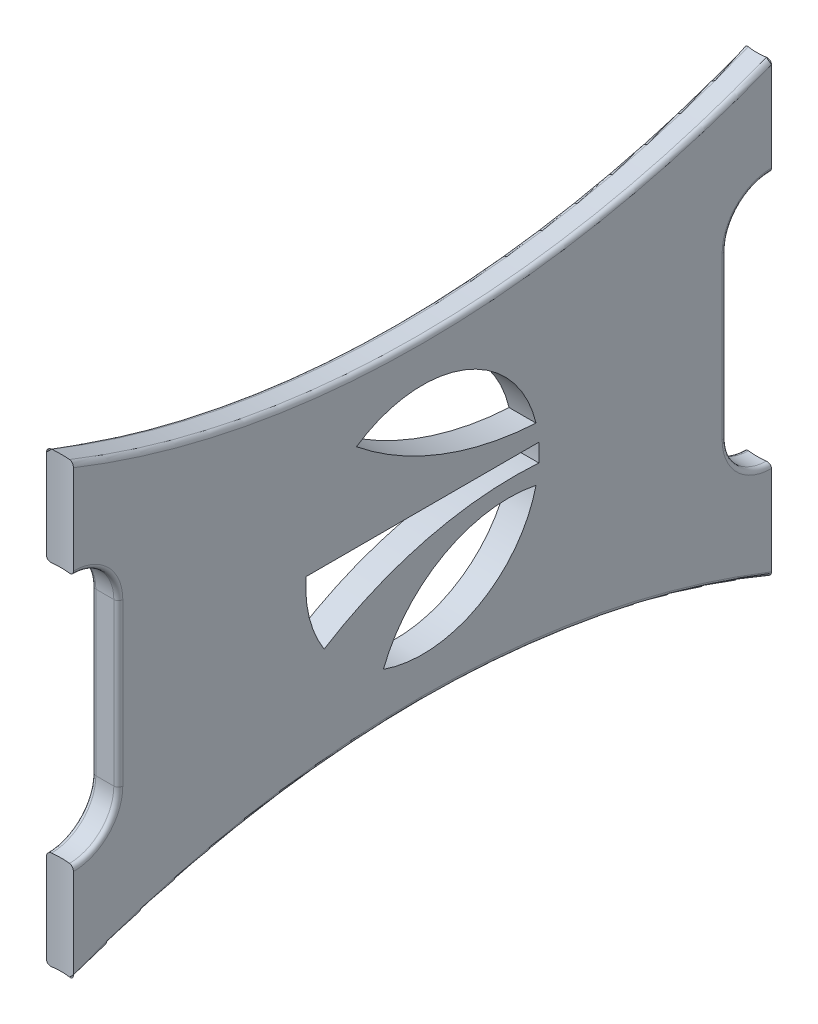
SolidWorks part; units mm, degrees
ref_plane "Plan de face" through (0, 0, 0) normal (0, 0, 1) x (1, 0, 0)
ref_plane "Plan de dessus" through (0, 0, 0) normal (0, 1, 0) x (1, 0, 0)
ref_plane "Plan de droite" through (0, 0, 0) normal (1, 0, 0) x (0, 0, -1)
sketch "Esquisse1" plane through (0, 0, 0) normal (0, 1, 0) x (1, 0, 0)
  line L0 (0, 0) -> (7.2264, 0) construction
  line L1 (0, 0) -> (0, 41.9928) construction
  line L4 (-1.5, 38.8834) -> (-1.5, -38.8834)
  line L6 (1.5, 38.8834) -> (1.5, -38.8834)
  arc A0 (-1.5, 38.8834) -> (1.5, 38.8834) centre (0, 47.25) ccw
  arc A1 (-1.5, -38.8834) -> (1.5, -38.8834) centre (0, -47.25) cw
  dimension "D2" = 8.5
  dimension "D3" = 94.5
  dimension "D1" = 3
extrude "Extrusion1" add sketch "Esquisse1" along normal mid plane 50
sketch "Esquisse2" plane through (1.5, 0, 0) normal (1, 0, 0) x (0, 0, -1)
  line L0 (-42.8055, 0) -> (42.8055, 0) construction
  line L1 (-38.8834, 25) -> (-38.8834, -25) construction
  line L2 (-33.8834, 9) -> (-33.8834, -9)
  line L3 (-38.8834, 14) -> (-38.8834, -14)
  line L4 (0, 28.2033) -> (0, -30.5585) construction
  line L5 (38.8834, 14) -> (38.8834, -14)
  line L6 (33.8834, 9) -> (33.8834, -9)
  line L7 (-38.8834, 25) -> (38.8834, 25)
  line L8 (-38.8834, -25) -> (38.8834, -25)
  arc A0 (38.8834, 25) -> (-38.8834, 25) centre (0, 122.0446) cw
  arc A1 (38.8834, -25) -> (-38.8834, -25) centre (0, -122.0446) ccw
  arc A2 (-33.8834, 9) -> (-38.8834, 14) centre (-38.8834, 9) ccw
  arc A3 (-33.8834, -9) -> (-38.8834, -14) centre (-38.8834, -9) cw
  arc A4 (33.8834, -9) -> (38.8834, -14) centre (38.8834, -9) ccw
  arc A5 (33.8834, 9) -> (38.8834, 14) centre (38.8834, 9) cw
  dimension "D1" = 35
  dimension "D2" = 5
  dimension "D3" = 28
extrude "Enlèv. mat.-Extru.1" cut sketch "Esquisse2" against normal through all
sketch "Esquisse3" plane through (1.5, 0, 0) normal (1, 0, 0) x (0, 0, -1)
  line L0 (-39.9793, 0) -> (39.9793, 0) construction
  line L1 (12.9615, 1) -> (-12.9615, 1)
  arc A0 (-12.9615, 1) -> (-10.9545, -7) centre (0, 0) ccw
  arc A1 (-7.3509, 10.7221) -> (12.6491, 3) centre (14.65, 37.9428) ccw
  arc A2 (12.6491, -3) -> (-4.3509, -12.2503) centre (9.6271, -17.6924) ccw
  arc A3 (12.9615, -1) -> (-10.9545, -7) centre (10.2632, -40.9089) ccw
  arc A4 (12.6491, 3) -> (-7.3509, 10.7221) centre (0, 0) ccw
  arc A5 (12.9615, -1) -> (12.9615, 1) centre (0, 0) ccw
  arc A6 (-4.3509, -12.2503) -> (12.6491, -3) centre (0, 0) ccw
  dimension "D1" = 26
  dimension "D6" = 35
  dimension "D9" = 15
  dimension "D11" = 40
  dimension "D2" = 1
  dimension "D3" = 2
  dimension "D4" = 3
  dimension "D5" = 20
  dimension "D7" = 17
  dimension "D8" = 3
  dimension "D10" = 8
extrude "Enlèv. mat.-Extru.2" cut sketch "Esquisse3" against normal through all
fillet "Congé1" radius 0.5 24 edges at (-1.5, 17.5, 0) (1.5, 17.5, 0) (-1.5, -17.5, 0) (1.5, -17.5, 0) (-1.5, 12.5355, 35.3479) (1.0271, 13.9995, 38.8123) (-1.0271, -13.9995, 38.8123) (-1.5, -12.5355, 35.3479) (-1.5, 0, 33.8834) (1.5, 12.5355, 35.3479) (1.5, -12.5355, 35.3479) (1.5, 0, 33.8834) (-1.5, -12.5355, -35.3479) (1.0271, -13.9995, -38.8123) (-1.0271, 13.9995, -38.8123) (-1.5, 12.5355, -35.3479) (-1.5, 0, -33.8834) (1.5, -12.5355, -35.3479) (1.5, 12.5355, -35.3479) (1.5, 0, -33.8834)
